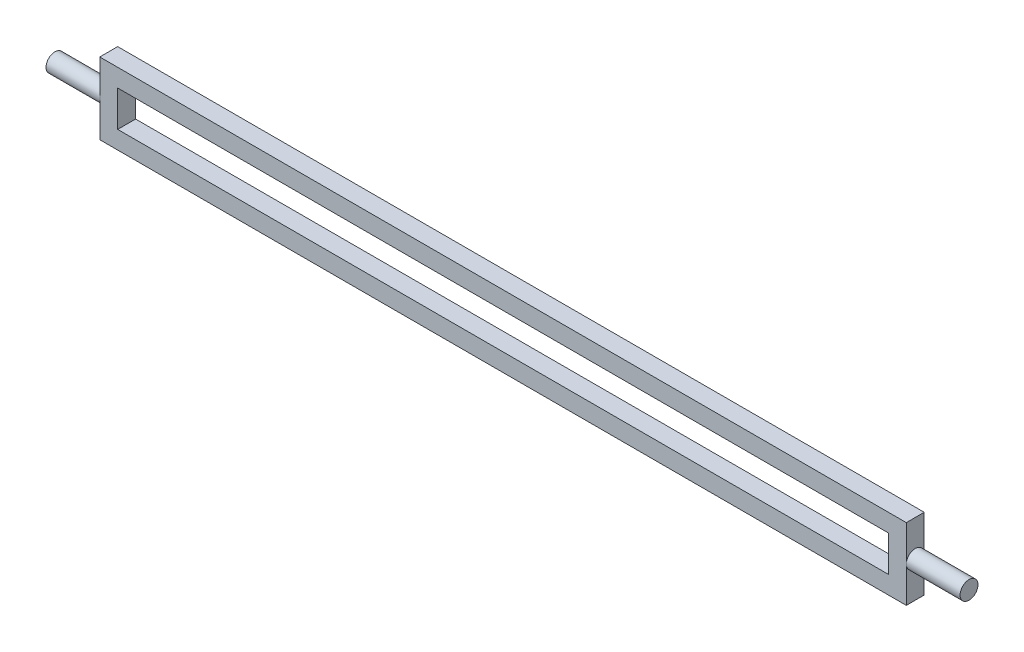
SolidWorks part; units mm, degrees
ref_plane "Front Plane" through (0, 0, 0) normal (0, 0, 1) x (1, 0, 0)
ref_plane "Top Plane" through (0, 0, 0) normal (0, 1, 0) x (1, 0, 0)
ref_plane "Right Plane" through (0, 0, 0) normal (1, 0, 0) x (0, 0, -1)
sketch "Sketch1" plane through (0, 0, 0) normal (0, 0, 1) x (1, 0, 0)
  line L1 (0, 0) -> (225, 0)
  line L2 (0, 0) -> (0, 20)
  line L3 (0, 20) -> (225, 20)
  line L4 (225, 0) -> (225, 20)
  dimension "D1" = 225
  dimension "D2" = 20
extrude "Boss-Extrude1" add sketch "Sketch1" along normal blind 5
sketch "Sketch2" plane through (225, 0, 0) normal (1, 0, 0) x (0, 0, -1)
  line L1 (0, 0) -> (0, 20) construction
  line L2 (-5, 0) -> (0, 0) construction
  circle A0 centre (-2.5, 10) radius 2.5
  point P2 (0, 0)
  point P5 (0, 0)
  point P6 (0, 10)
  point P9 (-2.5, 0)
extrude "Boss-Extrude2" add sketch "Sketch2" along normal blind 15
sketch "Sketch3" plane through (0, 0, 0) normal (-1, 0, 0) x (0, 0, 1)
  line L0 (5, 0) -> (0, 0) construction
  line L1 (5, 20) -> (5, 0) construction
  circle A0 centre (2.5, 10) radius 2.5
  point P5 (2.5, 0)
extrude "Boss-Extrude3" add sketch "Sketch3" along normal blind 15
sketch "Sketch4" plane through (0, 0, 5) normal (0, 0, 1) x (1, 0, 0)
  line L0 (220, 5) -> (220, 15)
  line L1 (0, 0) -> (225, 0) construction
  line L2 (0, 0) -> (0, 20) construction
  line L3 (0, 20) -> (225, 20) construction
  line L4 (225, 0) -> (225, 20) construction
  line L5 (5, 15) -> (220, 15)
  line L6 (5, 5) -> (5, 15)
  line L7 (5, 5) -> (220, 5)
  dimension "D1" = 5
extrude "Cut-Extrude1" cut sketch "Sketch4" against normal through all
